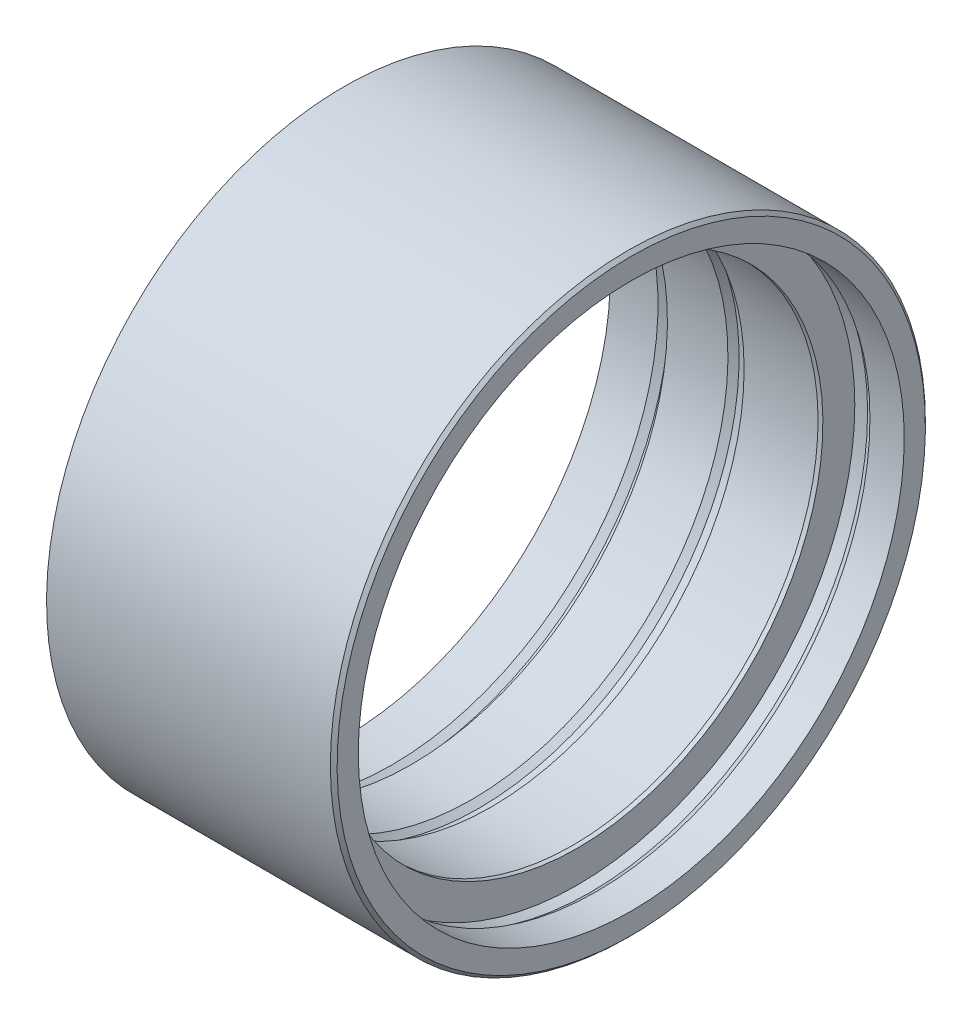
SolidWorks part; units mm, degrees
material "2018 slitina"
ref_plane "Přední rovina" through (0, 0, 0) normal (0, 0, 1) x (1, 0, 0)
ref_plane "Horní rovina" through (0, 0, 0) normal (0, 1, 0) x (1, 0, 0)
ref_plane "Pravá rovina" through (0, 0, 0) normal (1, 0, 0) x (0, 0, -1)
sketch "Skica2" plane through (0, 0, 0) normal (0, 0, 1) x (1, 0, 0)
  line L0 (-36.7133, -44.25) -> (6, -44.25)
  line L1 (6, -44.25) -> (6, -40.6)
  line L2 (6, -40.6) -> (0.9, -40.6)
  line L3 (-2, -36.5) -> (-2.7167, -36.5)
  line L4 (-2.7167, -36.5) -> (-2.8839, -37.6)
  line L5 (-2.8839, -37.6) -> (-14.8133, -37.6)
  line L6 (-14.8133, -37.6) -> (-14.8133, -38.75)
  line L7 (0, 0) -> (47.3772, 0) construction
  line L8 (-2, -36.5) -> (-2, -41.25)
  line L9 (-2, -41.25) -> (-0.1, -41.25)
  line L10 (-0.1, -41.25) -> (0.9, -40.6)
  line L11 (-14.8133, -38.75) -> (-16.7133, -38.75)
  line L12 (-16.7133, -38.75) -> (-17.7133, -38.094)
  line L13 (-17.7133, -38.094) -> (-26.7133, -38.094)
  line L14 (-26.7133, -38.094) -> (-26.7133, -40.25)
  line L15 (-26.7133, -40.25) -> (-28.6133, -40.25)
  line L16 (-28.6133, -40.25) -> (-29.6133, -39.594)
  line L17 (-29.6133, -39.594) -> (-36.7133, -39.594)
  line L18 (-36.7133, -39.594) -> (-36.7133, -44.25)
  line L19 (6, -40.6) -> (19.622, -44.25) construction
  line L20 (19.622, -44.25) -> (6, -44.25) construction
  arc A0 (-2.8691, -37.5) -> (-2.8691, 37.5) centre (-246.5, 0) ccw construction
  arc A1 (-2.8691, -37.5) -> (-2.8691, 37.5) centre (-246.5, 0) ccw construction
  point P0 (-15.7633, -38.75)
  point P11 (-2.8003, -37.05)
  dimension "D6" = 6
  dimension "D1" = 0.1
  dimension "D2" = 81.2
  dimension "D3" = 82.5
  dimension "D4" = 1.9
  dimension "D5" = 2.9
  dimension "D7" = 8
  dimension "D8" = 73
  dimension "D9" = 1.9
  dimension "D10" = 2.9
  dimension "D11" = 2
  dimension "D12" = 76.188
  dimension "D13" = 11
  dimension "D14" = 77.5
  dimension "D15" = 1.9
  dimension "D16" = 2.9
  dimension "D17" = 10
  dimension "D18" = 80.5
  dimension "D19" = 79.188
  dimension "D20" = 4
  dimension "D21" = 15
revolve "Rotovat1" add sketch "Skica2" angle 360 about L7
cosmetic thread "Kosmetický závit1" parameters "D2"=82
cosmetic thread "Kosmetický závit4" parameters "D2"=78
cosmetic thread "Kosmetický závit5" parameters "D2"=80
chamfer "Zkosení1" distance 0.5 angle 45 1 edges at (6, -44.25, 0)
